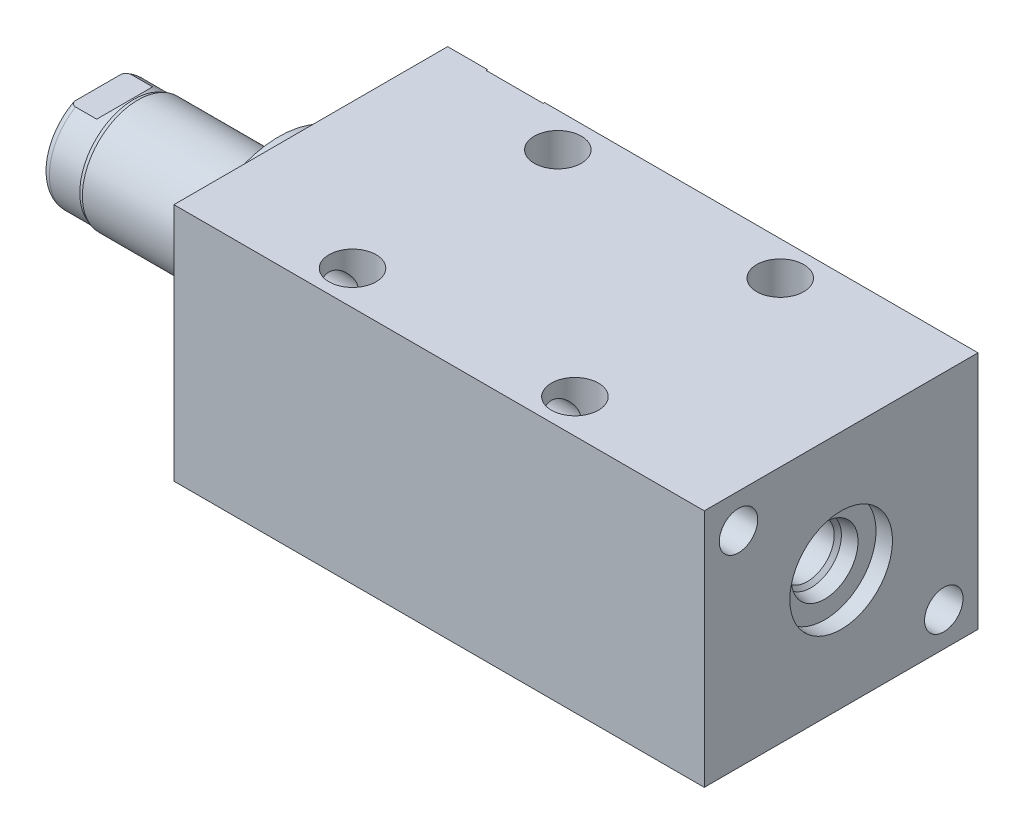
SolidWorks part; units mm, degrees
material "Alloy Steel"
ref_plane "Front Plane" through (0, 0, 0) normal (0, 0, 1) x (1, 0, 0)
ref_plane "Top Plane" through (0, 0, 0) normal (0, 1, 0) x (1, 0, 0)
ref_plane "Right Plane" through (0, 0, 0) normal (1, 0, 0) x (0, 0, -1)
ref_plane "Plane1" through (0, 0, 0) normal (1, 0, 0) x (0, 0, -1)
sketch "Sketch1" plane through (0, 0, 0) normal (1, 0, 0) x (0, 0, -1)
  line L0 (-25.4, 22.225) -> (25.4, 22.225)
  line L1 (25.4, 22.225) -> (25.4, -22.225)
  line L2 (25.4, -22.225) -> (-25.4, -22.225)
  line L3 (-25.4, -22.225) -> (-25.4, 22.225)
  line L4 (0, -24.4475) -> (0, 24.4475) construction
  dimension "D1" = 44.45
  dimension "D2" = 22.225
  dimension "D3" = 50.8
extrude "Extrude1" add sketch "Sketch1" along normal blind 98.425
ref_plane "Plane12" through (0, 14.3002, 0) normal (0, 1, 0) x (-1, 0, 0)
sketch "S2D0002" plane through (0, 14.3002, 0) normal (0, 1, 0) x (-1, 0, 0)
  line L0 (-18.8849, -25.146) -> (-22.225, -25.146)
  line L1 (-18.8849, -25.146) -> (-18.3423, -22.5933)
  line L2 (-18.3423, -22.5933) -> (-17.6784, -21.9294)
  line L3 (-17.6784, -21.9294) -> (-17.6784, -11.176)
  line L4 (-17.6784, -11.176) -> (-12.7, -11.176)
  line L5 (-12.7, -11.176) -> (-12.7, -25.4)
  line L6 (-12.7, -19.1384) -> (-12.7, 0.6985) construction
  line L7 (0, -25.4) -> (0, 25.4) construction
  line L8 (-22.225, -25.4) -> (-22.225, -25.146)
  line L9 (-98.425, -25.4) -> (0, -25.4) construction
  line L10 (-22.225, -25.4) -> (-12.7, -25.4)
  dimension "D1" = 14.224
  dimension "D2" = 12.7
  dimension "D3" = 9.9568
  dimension "D4" = 45
  dimension "D5" = 12.3698
  dimension "D6" = 12
  dimension "D7" = 2.5527
  dimension "D8" = 0.254
  dimension "D9" = 19.05
revolve "Cut-Revolve1" cut sketch "S2D0002" angle 360 about L6
ref_plane "Plane3" through (41.148, 0, -25.146) normal (0, 1, 0) x (1, 0, 0)
sketch "Sketch3" plane through (41.148, 0, -25.146) normal (0, 1, 0) x (1, 0, 0)
  line L0 (47.5869, 0) -> (50.927, 0)
  line L1 (47.5869, 0) -> (47.0443, -2.5527)
  line L2 (47.0443, -2.5527) -> (46.3804, -3.2166)
  line L3 (46.3804, -3.2166) -> (46.3804, -13.97)
  line L4 (46.3804, -13.97) -> (41.402, -13.97)
  line L5 (41.402, -13.97) -> (41.402, 0.254)
  line L6 (41.402, -21.9564) -> (41.402, 0.6985) construction
  line L7 (-41.148, 0.254) -> (-41.148, -50.546) construction
  line L8 (50.927, 0.254) -> (50.927, 0)
  line L9 (57.277, 0.254) -> (-23.1638, 0.254) construction
  line L10 (50.927, 0.254) -> (41.402, 0.254)
  dimension "D1" = 14.224
  dimension "D2" = 82.55
  dimension "D3" = 9.9568
  dimension "D4" = 45
  dimension "D5" = 12
  dimension "D6" = 12.3698
  dimension "D7" = 2.5527
  dimension "D8" = 0.254
  dimension "D9" = 19.05
revolve "Cut-Revolve2" cut sketch "Sketch3" angle 360 about L6
ref_plane "Plane4" through (53.975, 0, 0) normal (0, 0, 1) x (0, -1, 0)
sketch "Sketch4" plane through (53.975, 0, 0) normal (0, 0, 1) x (0, -1, 0)
  line L0 (6.1849, 41.402) -> (9.525, 41.402)
  line L1 (6.1849, 41.402) -> (5.6423, 38.8493)
  line L2 (5.6423, 38.8493) -> (4.9784, 38.1854)
  line L3 (4.9784, 38.1854) -> (4.9784, 30.0482)
  line L4 (4.9784, 30.0482) -> (0, 30.0482)
  line L5 (0, 30.0482) -> (0, 44.45)
  line L6 (0, -15.0954) -> (0, 0.5677) construction
  line L7 (0, 44.45) -> (9.525, 44.45)
  line L9 (-22.225, 44.45) -> (22.225, 44.45) construction
  line L10 (9.525, 44.45) -> (9.525, 41.402)
  dimension "D1" = 11.3538
  dimension "D2" = 9.9568
  dimension "D3" = 3.048
  dimension "D4" = 19.05
  dimension "D5" = 2.5527
  dimension "D6" = 12
  dimension "D7" = 45
  dimension "D8" = 12.3698
revolve "Cut-Revolve3" cut sketch "Sketch4" angle 360 about L6
sketch "Sketch5" plane through (0, 0, 0) normal (-1, 0, 0) x (0, 0, 1)
  circle A0 centre (0, 0) radius 17.4625
  dimension "D1" = 34.925
extrude "Extrude2" add sketch "Sketch5" along normal blind 5.969
ref_plane "Plane5" through (0, 0, 0) normal (0, -1, 0) x (0, 0, 1)
sketch "Sketch6" plane through (0, 0, 0) normal (0, -1, 0) x (0, 0, 1)
  line L0 (0, 5.969) -> (-10.3187, 5.969)
  line L1 (-10.3187, 5.969) -> (-10.3187, 39.497)
  line L2 (-10.3187, 39.497) -> (0, 39.497)
  line L3 (0, 39.497) -> (0, 5.969)
  line L4 (0, -5.7546) -> (0, 21.1709) construction
  line L5 (17.4625, 5.969) -> (-17.4625, 5.969) construction
  line L6 (25.4, -98.425) -> (-25.4, -98.425) construction
  dimension "D1" = 137.922
  dimension "D2" = 20.6375
revolve "Revolve1" add sketch "Sketch6" angle 360 about L4
ref_plane "Plane6" through (-18.5113, 3.2639, 0) normal (0, 0, 1) x (0, 1, 0)
sketch "S2D0001" plane through (-18.5113, 3.2639, 0) normal (0, 0, 1) x (0, 1, 0)
  line L0 (0, 19.05) -> (0, 5.9235)
  line L1 (0, 5.9235) -> (-3.2639, 5.9235)
  line L2 (1.1176, 20.9857) -> (-3.2639, 20.9857)
  line L3 (-3.2639, 20.9857) -> (-3.2639, 5.9235)
  line L4 (0, 19.05) -> (1.1176, 20.9857)
  line L5 (-3.2639, -18.5113) -> (-3.2639, 2.765) construction
  line L6 (7.0549, 20.9857) -> (-13.5826, 20.9857) construction
  dimension "D1" = 30
  dimension "D2" = 8.763
  dimension "D3" = 6.5278
  dimension "D4" = 15.0622
revolve "Cut-Revolve4" cut sketch "S2D0001" angle 360 about L5
ref_plane "Plane7" through (0, 0, 0) normal (0, 1, 0) x (0, 0, -1)
sketch "Sketch8" plane through (0, 0, 0) normal (0, 1, 0) x (0, 0, -1)
  line L0 (-10.3187, 32.0802) -> (-10.033, 32.8422)
  line L1 (-10.033, 32.8422) -> (-10.033, 38.481)
  line L2 (0, 12.6594) -> (0, 20.8178) construction
  line L3 (-10.3187, 32.0802) -> (-10.3187, 39.497)
  line L4 (-9.6449, 39.497) -> (-10.3187, 39.497)
  line L5 (10.3187, 39.497) -> (-10.3187, 39.497) construction
  line L6 (-10.3187, 39.497) -> (-10.3187, 5.969) construction
  arc A0 (-9.6449, 39.497) -> (-10.033, 38.481) centre (-8.509, 38.481) ccw
  dimension "D2" = 1.524
  dimension "D1" = 20.066
  dimension "D3" = 1.016
  dimension "D4" = 0.762
  dimension "D5" = 6.6548
revolve "Cut-Revolve5" cut sketch "Sketch8" angle 360 about L2
ref_plane "Plane11" through (0, 0, 0) normal (0, 0, -1) x (0, -1, 0)
sketch "Sketch12" plane through (0, 0, 0) normal (0, 0, -1) x (0, -1, 0)
  line L0 (8.5852, 39.497) -> (8.5852, 34.544)
  line L1 (8.5852, 34.544) -> (10.033, 33.0962)
  line L2 (-8.5852, 39.497) -> (-8.5852, 34.544)
  line L3 (-8.5852, 34.544) -> (-10.033, 33.0962)
  line L4 (8.5852, 39.497) -> (10.033, 39.497)
  line L5 (0, 13.7262) -> (0, 20.767) construction
  line L6 (-10.033, 33.0962) -> (-10.033, 39.497)
  line L7 (9.6449, 39.497) -> (-9.6449, 39.497) construction
  line L8 (10.033, 32.8422) -> (10.033, 38.481) construction
  line L9 (10.033, 33.0962) -> (10.033, 39.497)
  line L10 (-8.5852, 39.497) -> (-10.033, 39.497)
  dimension "D1" = 17.1704
  dimension "D2" = 4.953
  dimension "D3" = 45
extrude "Cut-Extrude4" cut sketch "Sketch12" against normal mid plane 60.96
hole_wizard "Hole1" positions "Sketch15" profile "Sketch14" legacy end condition up to next
sketch "Sketch15" plane through (0, 0, 0) normal (-1, 0, 0) x (0, 0, 1)
  line L0 (0, 0) -> (-29.9914, 0) construction
  line L1 (0, 0) -> (0, 25.7648) construction
  point P0 (-19.05, -15.875)
  point P11 (19.05, 15.875)
  dimension "D1" = 15.875
  dimension "D2" = 19.05
  dimension "D3" = 31.75
  dimension "D4" = 38.1
sketch "Sketch14" plane through (0, -15.875, -19.05) normal (0, 1, 0) x (0, 0, 1)
  line L0 (0, 0) -> (0, 98.425)
  line L1 (0, 98.425) -> (3.5687, 98.425)
  line L2 (3.5687, 98.425) -> (3.5687, 0)
  line L3 (3.5687, 0) -> (0, 0)
  line L4 (0, 110) -> (0, -10) construction
  dimension "Diameter" = 7.1374
  dimension "Depth" = 98.425
hole_wizard "Hole2" positions "Sketch17" profile "Sketch16" legacy
sketch "Sketch17" plane through (0, 22.225, 0) normal (0, 1, 0) x (-1, 0, 0)
  line L0 (0, 0) -> (-59.3363, 0) construction
  line L1 (0, -25.4) -> (0, 25.4) construction
  point P0 (-26.797, -19.05)
  point P9 (-26.797, 19.05)
  dimension "D1" = 38.1
  dimension "D2" = 26.797
sketch "Sketch16" plane through (26.797, 22.225, -19.05) normal (1, 0, 0) x (0, 0, 1)
  line L0 (0, 0) -> (0, 44.45)
  line L1 (0, 44.45) -> (4.3688, 44.45)
  line L2 (4.3688, 44.45) -> (4.3688, 0)
  line L3 (4.3688, 0) -> (0, 0)
  line L4 (0, 110) -> (0, -10) construction
  dimension "Diameter" = 8.7376
  dimension "Depth" = 44.45
pattern_linear "LPattern1" count 2 spacing 41.275 along (1, 0, 0) of "Hole2"
